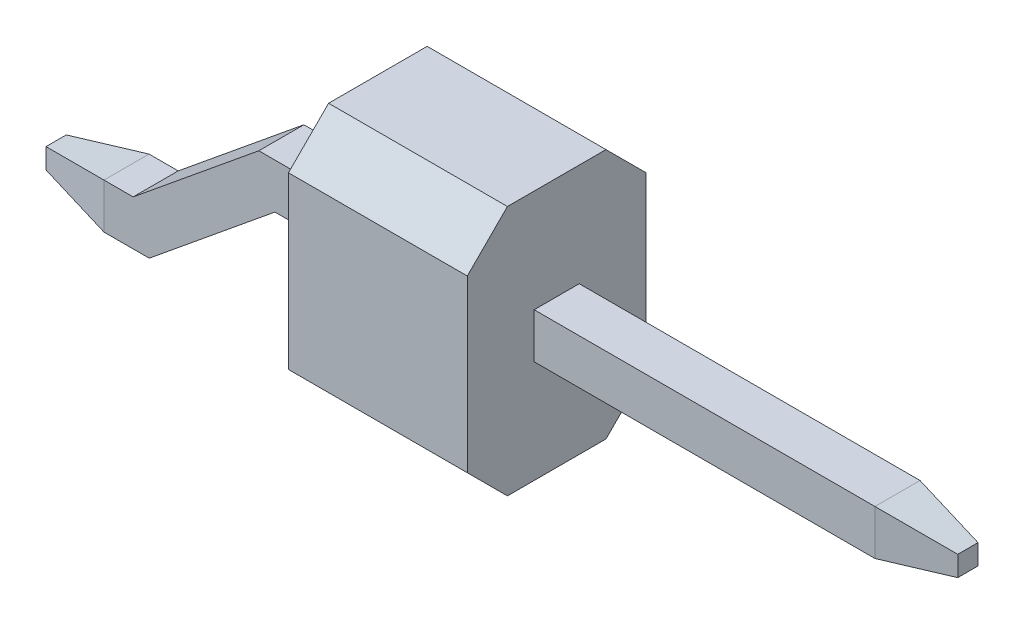
SolidWorks part; units mm, degrees
ref_plane "Front Plane" through (0, 0, 0) normal (0, 0, 1) x (1, 0, 0)
ref_plane "Top Plane" through (0, 0, 0) normal (0, 1, 0) x (1, 0, 0)
ref_plane "Right Plane" through (0, 0, 0) normal (1, 0, 0) x (0, 0, -1)
sketch "Sketch1" plane through (0, 0, 0) normal (0, 1, 0) x (1, 0, 0)
  line L1 (0, 0) -> (2.54, 0)
  line L2 (0, 0) -> (0, 2.54)
  line L3 (0, 2.54) -> (2.54, 2.54)
  line L4 (2.54, 0) -> (2.54, 2.54)
  dimension "D1" = 2.54
  dimension "D2" = 2.54
extrude "Boss-Extrude1" add sketch "Sketch1" along normal blind 3.56
sketch "Sketch2" plane through (2.54, 0, 0) normal (1, 0, 0) x (0, 0, -1)
  line L1 (0.95, 2.1) -> (1.59, 2.1)
  line L2 (0.95, 2.1) -> (0.95, 1.46)
  line L3 (0.95, 1.46) -> (1.59, 1.46)
  line L4 (1.59, 2.1) -> (1.59, 1.46)
  line L5 (1.27, 2.1) -> (1.27, 3.56) construction
  line L6 (0, 3.56) -> (2.54, 3.56) construction
  line L7 (0.95, 1.78) -> (0, 1.78) construction
  line L8 (0, 3.56) -> (0, 0) construction
  line L9 (0, 0) -> (2.54, 0)
  line L10 (2.54, 0) -> (2.54, 3.56)
  line L11 (2.54, 3.56) -> (0, 3.56)
  line L12 (0, 3.56) -> (0, 0)
  line L13 (0, 0) -> (2.54, 0) construction
  line L14 (2.54, 0) -> (2.54, 3.56) construction
  line L15 (2.54, 3.56) -> (0, 3.56) construction
  line L16 (0, 3.56) -> (0, 0) construction
  dimension "D2" = 0.64
  dimension "D1" = 0
extrude "Boss-Extrude2" add sketch "Sketch2" along normal blind 5.84
chamfer "Chamfer1" distance 0.57 angle 45 4 edges at (1.27, 0, -2.54) (1.27, 0, 0) (1.27, 3.56, -2.54) (1.27, 3.56, 0)
chamfer "Chamfer2" distance 1 angle 10 4 edges at (8.38, 2.1, -1.27) (8.38, 1.78, -1.59) (8.38, 1.46, -1.27) (8.38, 1.78, -0.95)
sketch "Sketch3" plane through (0, 0, 0) normal (-1, 0, 0) x (0, 0, 1)
  line L0 (-0.95, 2.1) -> (-0.95, 1.46) construction
  line L1 (-0.95, 1.46) -> (-1.59, 1.46) construction
  line L2 (-1.59, 2.1) -> (-0.95, 2.1) construction
  line L3 (-1.59, 1.46) -> (-1.59, 2.1) construction
  line L4 (-0.95, 2.1) -> (-0.95, 1.46)
  line L5 (-0.95, 1.46) -> (-1.59, 1.46)
  line L6 (-1.59, 2.1) -> (-0.95, 2.1)
  line L7 (-1.59, 1.46) -> (-1.59, 2.1)
extrude "Boss-Extrude3" add sketch "Sketch3" along normal blind 2.285
sketch "Sketch4" plane through (-2.285, 0, 0) normal (-1, 0, 0) x (0, 0, 1)
  line L1 (-1.59, 1.46) -> (-0.95, 1.46) construction
  line L2 (-0.95, 0) -> (-1.59, 0)
  line L3 (-0.95, 0) -> (-0.95, 0.64)
  line L4 (-0.95, 0.64) -> (-1.59, 0.64)
  line L5 (-1.59, 0) -> (-1.59, 0.64)
  line L6 (-1.59, 2.1) -> (-1.59, 1.46) construction
  line L7 (-1.97, 0) -> (-0.57, 0) construction
extrude "Boss-Extrude4" add sketch "Sketch4" along normal blind 2.285 separate body
chamfer "Chamfer3" distance 1 angle 10 4 edges at (-4.57, 0, -1.27) (-4.57, 0.32, -1.59) (-4.57, 0.64, -1.27) (-4.57, 0.32, -0.95)
sketch "Sketch5" plane through (0, 0, -1.59) normal (0, 0, -1) x (-1, 0, 0)
  line L1 (2.285, 0.5255) -> (1.1425, 1.46)
  line L2 (2.285, 1.46) -> (0, 1.46) construction
  line L3 (3.1559, 0.64) -> (2.1534, 1.46)
  line L4 (3.3327, 0.4954) -> (1.5477, 1.9554) construction
  line L5 (3.57, 0.64) -> (2.285, 0.64) construction
  line L6 (1.1425, 1.46) -> (2.1534, 1.46)
  line L7 (2.285, 0.64) -> (3.1559, 0.64)
  line L8 (2.285, 0.64) -> (2.285, 0.5255)
  line L9 (2.285, 0.64) -> (2.285, 0) construction
  line L10 (2.285, 0.5255) -> (2.9275, 0) construction
  line L11 (2.9275, 0) -> (1.1425, 1.46) construction
  line L12 (3.57, 0) -> (2.285, 0) construction
  dimension "D1" = 0.64
extrude "Boss-Extrude5" add sketch "Sketch5" against normal up to surface (0.64 mm away) up to face at (-1.1425, 1.78, -0.95)
sketch "Sketch6" plane through (0, 0, -1.59) normal (0, 0, -1) x (-1, 0, 0)
  line L0 (3.1559, 0.64) -> (2.1534, 1.46) construction
  line L1 (2.1534, 1.46) -> (1.3709, 2.1)
  line L2 (2.285, 2.1) -> (0, 2.1) construction
  line L3 (2.285, 2.1) -> (2.285, 1.46) construction
  line L4 (2.285, 1.46) -> (2.1534, 1.46) construction
  line L5 (2.285, 2.1) -> (2.285, 1.46)
  line L6 (2.285, 1.46) -> (2.1534, 1.46)
  line L7 (1.3709, 2.1) -> (2.285, 2.1)
  line L8 (1.1425, 1.46) -> (2.285, 0.5255) construction
  line L9 (2.285, 0.5255) -> (2.9275, 0)
  line L10 (3.57, 0) -> (2.285, 0) construction
  line L11 (2.285, 0.5255) -> (2.285, 0) construction
  line L12 (2.285, 0.5255) -> (2.285, 0)
  line L13 (2.285, 0) -> (2.9275, 0)
extrude "Cut-Extrude1" cut sketch "Sketch6" against normal through all both and the other way through all
